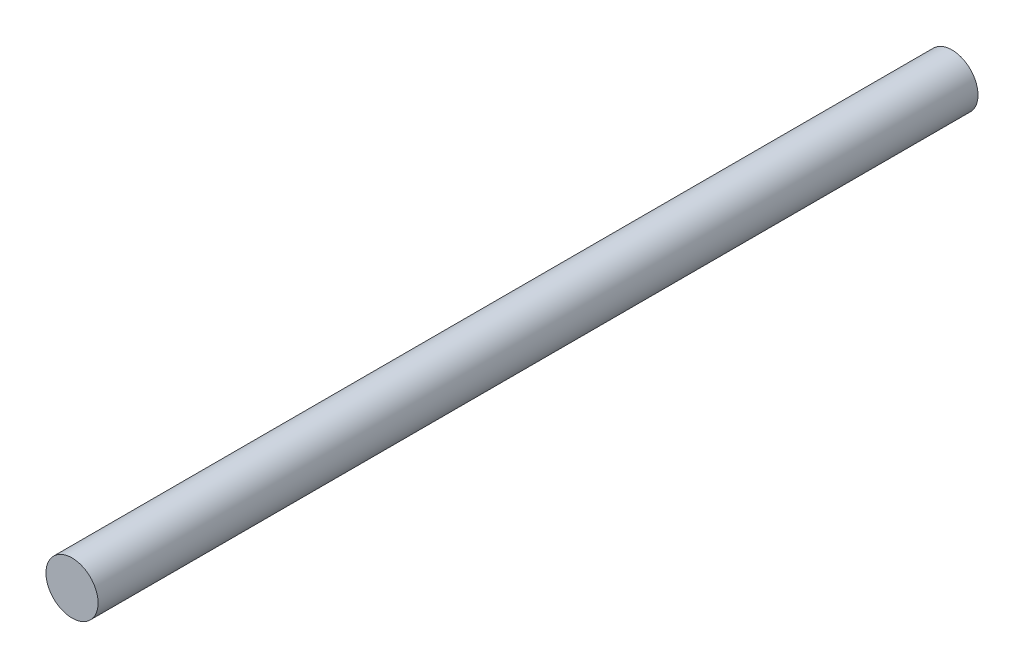
SolidWorks part; units mm, degrees
ref_plane "Front Plane" through (0, 0, 0) normal (0, 0, 1) x (1, 0, 0)
ref_plane "Top Plane" through (0, 0, 0) normal (0, 1, 0) x (1, 0, 0)
ref_plane "Right Plane" through (0, 0, 0) normal (1, 0, 0) x (0, 0, -1)
sketch "Sketch1" plane through (0, 0, 0) normal (0, 0, 1) x (1, 0, 0)
  circle A0 centre (0, 0) radius 4
  dimension "D1" = 8
extrude "Boss-Extrude1" add sketch "Sketch1" along normal blind 135
move or copy body "Body-Move/Copy1" [suppressed] bodies to move or copy 101
